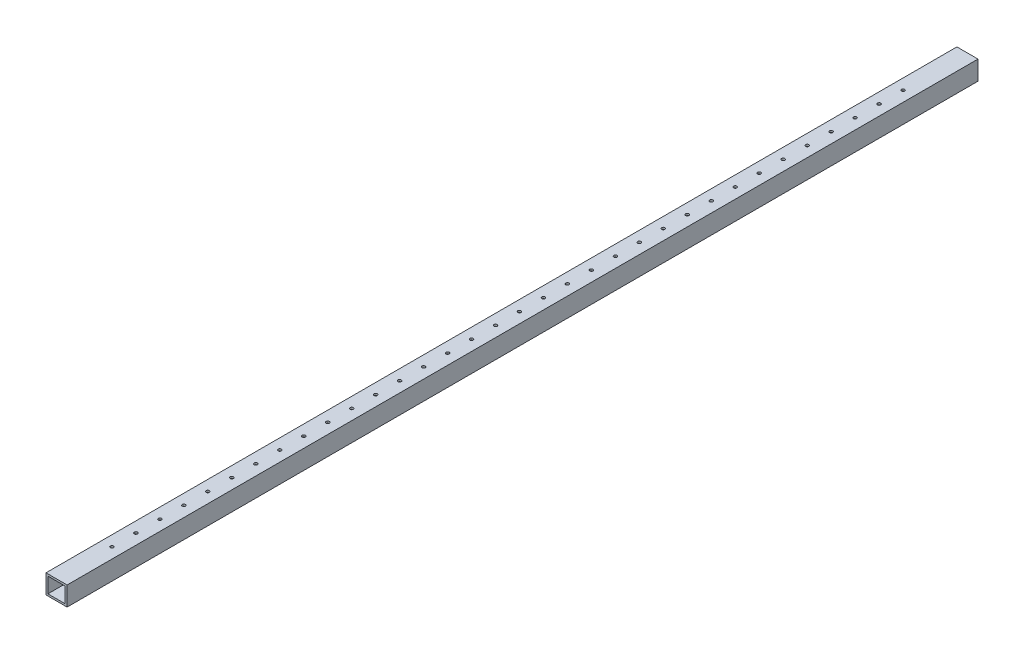
SolidWorks part; units mm, degrees
ref_plane "Front Plane" through (0, 0, 0) normal (0, 0, 1) x (1, 0, 0)
ref_plane "Top Plane" through (0, 0, 0) normal (0, 1, 0) x (1, 0, 0)
ref_plane "Right Plane" through (0, 0, 0) normal (1, 0, 0) x (0, 0, -1)
sketch "Sketch2" plane through (0, 0, 0) normal (0, 0, 1) x (1, 0, 0)
  line L1 (-19.9719, 18.0335) -> (20.0281, 18.0335)
  line L2 (-19.9719, 18.0335) -> (-19.9719, -17.9886)
  line L3 (-19.9719, -17.9886) -> (20.0281, -17.9886)
  line L4 (20.0281, 18.0335) -> (20.0281, -17.9886)
  line L5 (-19.9719, 18.0335) -> (20.0281, -17.9886) construction
  line L6 (-19.9719, -17.9886) -> (20.0281, 18.0335) construction
  point P0 (0.0281, 0.0225)
  dimension "D1" = 40
extrude "Extrude-Thin1" add sketch "Sketch2" along normal mid plane 1900 thin contours L2 L1 L4 L3 thin type mid plane wall 4
sketch "Sketch3" plane through (0, 20.0335, 0) normal (0, 1, 0) x (1, 0, 0)
  circle A0 centre (0, 815.6525) radius 3.35
  circle A1 centre (0, 765.6525) radius 3.35
  circle A2 centre (0, 715.6525) radius 3.35
  circle A3 centre (0, 665.6525) radius 3.35
  circle A4 centre (0, 615.6525) radius 3.35
  circle A5 centre (0, 565.6525) radius 3.35
  circle A6 centre (0, 515.6525) radius 3.35
  circle A7 centre (0, 465.6525) radius 3.35
  circle A8 centre (0, 415.6525) radius 3.35
  circle A9 centre (0, 365.6525) radius 3.35
  circle A10 centre (0, 315.6525) radius 3.35
  circle A11 centre (0, 265.6525) radius 3.35
  circle A12 centre (0, 215.6525) radius 3.35
  circle A13 centre (0, 165.6525) radius 3.35
  circle A14 centre (0, 115.6525) radius 3.35
  circle A15 centre (0, 65.6525) radius 3.35
  circle A16 centre (0, 15.6525) radius 3.35
  circle A17 centre (0, -34.3475) radius 3.35
  circle A18 centre (0, -84.3475) radius 3.35
  circle A19 centre (0, -134.3475) radius 3.35
  circle A20 centre (0, -184.3475) radius 3.35
  circle A21 centre (0, -234.3475) radius 3.35
  circle A22 centre (0, -284.3475) radius 3.35
  circle A23 centre (0, -334.3475) radius 3.35
  circle A24 centre (0, -384.3475) radius 3.35
  circle A25 centre (0, -434.3475) radius 3.35
  circle A26 centre (0, -484.3475) radius 3.35
  circle A27 centre (0, -534.3475) radius 3.35
  circle A28 centre (0, -584.3475) radius 3.35
  circle A29 centre (0, -634.3475) radius 3.35
  circle A30 centre (0, -684.3475) radius 3.35
  circle A31 centre (0, -734.3475) radius 3.35
  circle A32 centre (0, -784.3475) radius 3.35
  circle A33 centre (0, -834.3475) radius 3.35
  dimension "D1" = 34
  dimension "D2" = 6.7
extrude "Cut-Extrude1" cut sketch "Sketch3" against normal through all
